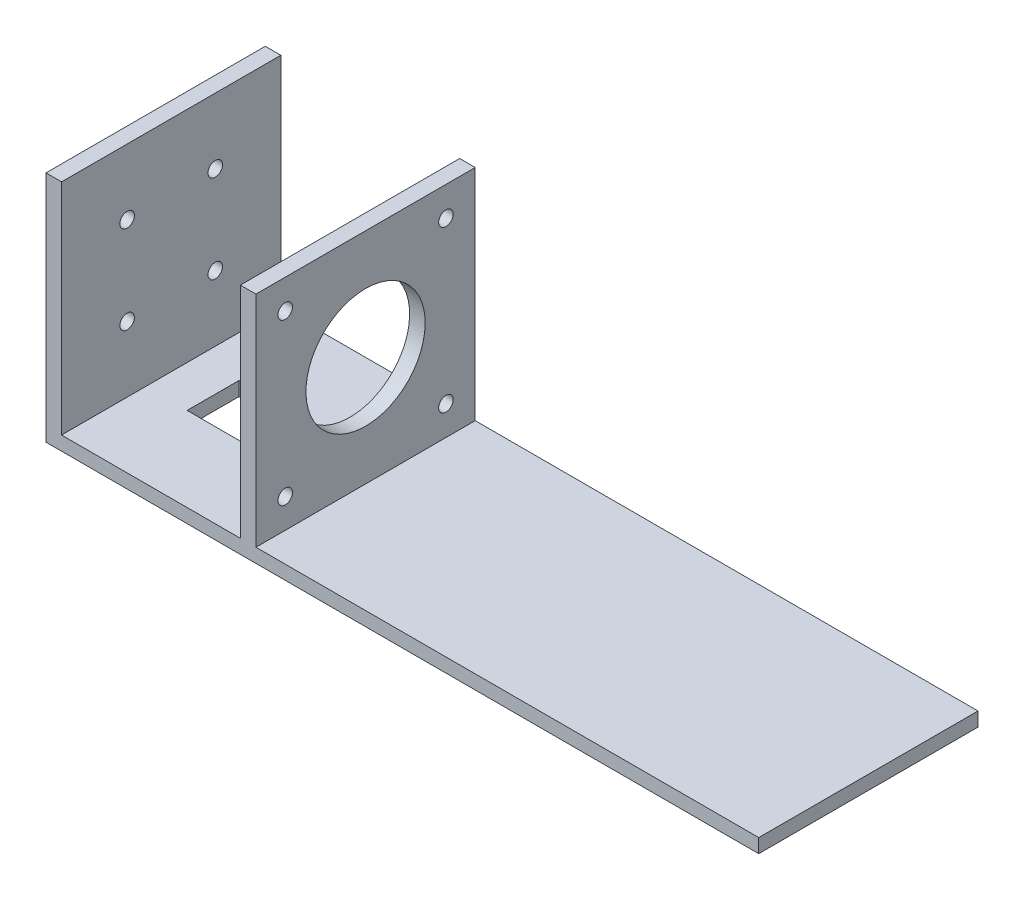
SolidWorks part; units mm, degrees
ref_plane "Front Plane" through (0, 0, 0) normal (0, 0, 1) x (1, 0, 0)
ref_plane "Top Plane" through (0, 0, 0) normal (0, 1, 0) x (1, 0, 0)
ref_plane "Right Plane" through (0, 0, 0) normal (1, 0, 0) x (0, 0, -1)
sketch "Sketch2" plane through (0, 0, 0) normal (0, 0, 1) x (1, 0, 0)
  line L0 (-2.75, 22.5) -> (-2.75, -19.8)
  line L1 (-40.25, 22.5) -> (-37.25, 22.5)
  line L2 (-40.25, 22.5) -> (-40.25, -22.5)
  line L3 (-40.25, -22.5) -> (97.25, -22.5)
  line L4 (97.25, -19.8) -> (97.25, -22.5)
  line L6 (-2.75, 22.5) -> (0.25, 22.5)
  line L7 (-27.25, 22.5) -> (-27.25, -19.8) construction
  line L8 (-29.25, 22.5) -> (-29.25, -19.8) construction
  line L9 (-37.25, 22.5) -> (-37.25, -19.8) construction
  line L10 (-37.25, -19.8) -> (-2.75, -19.8) construction
  line L11 (0.25, 22.5) -> (0.25, -19.8)
  line L12 (-37.25, 22.5) -> (-37.25, -19.8)
  line L13 (-37.25, -19.8) -> (-2.75, -19.8)
  line L15 (0.25, -19.8) -> (97.25, -19.8) construction
  line L16 (0.25, -19.8) -> (97.25, -19.8)
  line L18 (0, 0) -> (0.25, -0.1398) construction
  line L19 (0, 0) -> (0.25, 0.1398) construction
  point P0 (0, 0)
  dimension "D1" = 100
  dimension "D2" = 24.5
  dimension "D4" = 2
  dimension "D5" = 8
  dimension "D6" = 3
  dimension "D7" = 2.7
  dimension "D8" = 3
extrude "Boss-Extrude1" add sketch "Sketch2" along normal blind 42.3
sketch "Sketch3" plane through (0.25, 0, 0) normal (1, 0, 0) x (0, 0, -1)
  line L0 (-42.3, 22.5) -> (0, -19.8) construction
  line L1 (0, 22.5) -> (-42.3, -19.8) construction
  line L2 (-42.3, 16.85) -> (0, 16.85) construction
  line L3 (-42.3, -19.8) -> (-42.3, 22.5) construction
  line L4 (0, -19.8) -> (0, 22.5) construction
  circle A0 centre (-21.15, 1.35) radius 11.5
  circle A1 centre (-36.65, 16.85) radius 1.4
  circle A2 centre (-5.65, 16.85) radius 1.4
  circle A3 centre (-5.65, -14.15) radius 1.4
  circle A4 centre (-36.65, -14.15) radius 1.4
  point P16 (-36.65, 16.85)
  point P28 (-21.15, 1.35)
  dimension "D1" = 23
  dimension "D4" = 2.8
  dimension "D2" = 15.5
  dimension "D3" = 15.5
  dimension "D5" = 4
extrude "Cut-Extrude1" cut sketch "Sketch3" against normal blind 5
ref_plane "Plane1" through (-37.25, 0, 0) normal (1, 0, 0) x (0, 0, -1)
sketch "Sketch4" plane through (-37.25, 0, 0) normal (1, 0, 0) x (0, 0, -1)
  line L0 (-42.3, 22.5) -> (0, -19.8) construction
  line L1 (0, 22.5) -> (-42.3, -19.8) construction
  line L7 (-29.65, 9.85) -> (-12.65, -7.15) construction
  line L8 (-29.65, -7.15) -> (-12.65, 9.85) construction
  circle A0 centre (-29.65, 9.85) radius 1.4
  circle A1 centre (-12.65, 9.85) radius 1.4
  circle A2 centre (-12.65, -7.15) radius 1.4
  circle A3 centre (-29.65, -7.15) radius 1.4
  point P8 (-21.15, 1.35)
  point P23 (-21.15, 1.35)
  dimension "D3" = 2.8
  dimension "D1" = 17
  dimension "D2" = 17
  dimension "D4" = 4
extrude "Cut-Extrude2" cut sketch "Sketch4" against normal blind 5
sketch "Sketch5" plane through (0, -19.8, 0) normal (0, 1, 0) x (1, 0, 0)
  line L0 (-48.2095, -21.15) -> (47.4601, -21.15) construction
  line L1 (-37.25, 10.4451) -> (-37.25, -54.1673) construction
  line L2 (-37.25, -23.265) -> (-37.25, 23.265) construction
  line L3 (-2.75, 9.9455) -> (-2.75, -53.1682) construction
  line L4 (-26.75, 10.4451) -> (-26.75, -52.5853) construction
  line L5 (-11.75, 10.4451) -> (-11.75, -52.5853) construction
  line L10 (-26.75, -21.0701) -> (-26.5902, -21.15) construction
  line L11 (-26.9098, -21.15) -> (-26.75, -21.0701) construction
  line L12 (-19.25, 10.4451) -> (-19.25, -52.5853) construction
  line L14 (-29.25, -16.0701) -> (-9.25, -16.0701)
  line L15 (-29.25, -16.0701) -> (-29.25, -26.0701)
  line L16 (-29.25, -26.0701) -> (-9.25, -26.0701)
  line L17 (-9.25, -16.0701) -> (-9.25, -26.0701)
  line L18 (-29.25, -16.0701) -> (-9.25, -26.0701) construction
  line L19 (-29.25, -26.0701) -> (-9.25, -16.0701) construction
  point P17 (-19.25, -21.0701)
  dimension "D1" = 24
  dimension "D2" = 15
  dimension "D3" = 7.5
  dimension "D4" = 20
  dimension "D5" = 10
extrude "Cut-Extrude3" cut sketch "Sketch5" against normal blind 5
